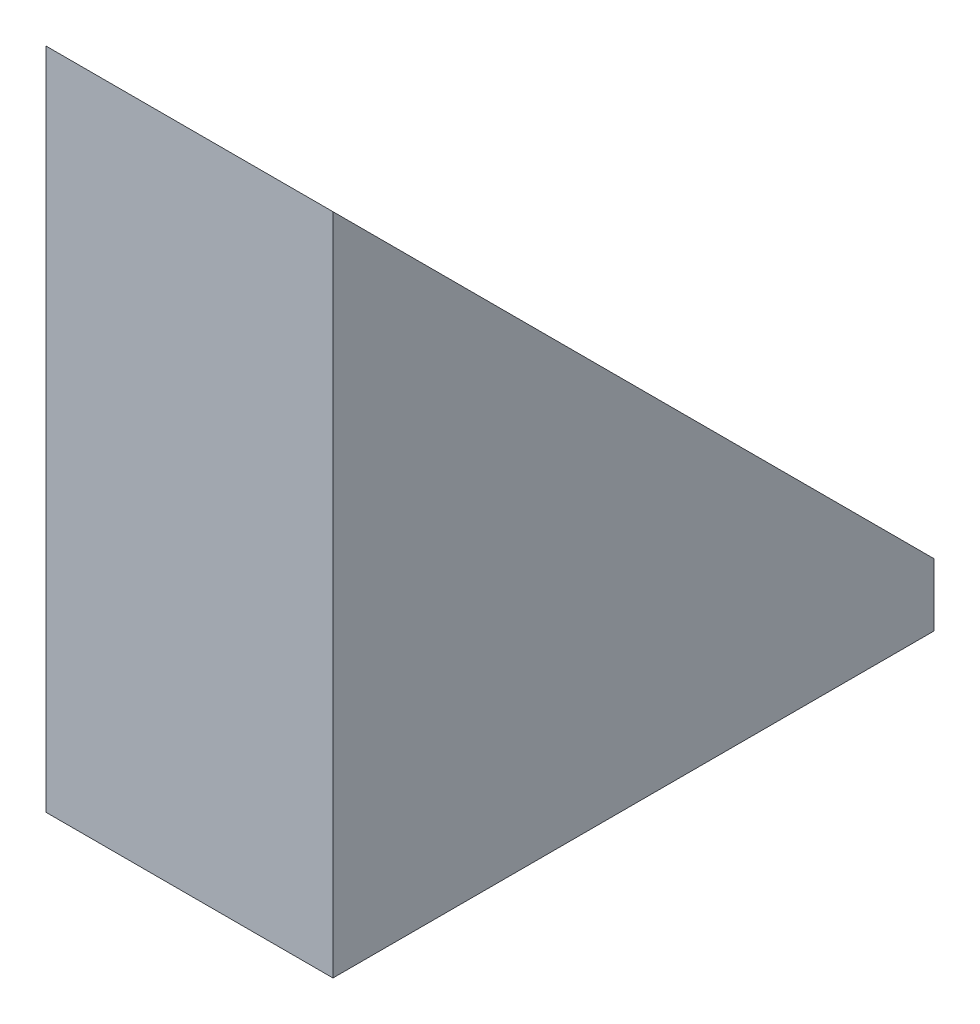
SolidWorks part; units mm, degrees
ref_plane "Plano frontal" through (0, 0, 0) normal (0, 0, 1) x (1, 0, 0)
ref_plane "Plano superior" through (0, 0, 0) normal (0, 1, 0) x (1, 0, 0)
ref_plane "Plano direito" through (0, 0, 0) normal (1, 0, 0) x (0, 0, -1)
sketch "Sketch1" plane through (-23229.7404, 0, 0) normal (-1, 0, 0) x (0, 0, 1)
  line L0 (40109.1002, 5310.5864) -> (40276.6536, 5478.1398)
  line L1 (40109.1002, 5293.1198) -> (40276.6536, 5293.1198)
  line L2 (40109.1002, 5293.1198) -> (40109.1002, 5310.5864)
  line L3 (40109.1002, 5310.5864) -> (40276.6536, 5310.5864)
  line L4 (40276.6536, 5293.1198) -> (40276.6536, 5310.5864)
  line L5 (40276.6536, 5478.1398) -> (40276.6536, 5310.5864)
  point P4 (40266.3788, 5450.5749)
  point P6 (40276.6536, 5478.1398)
  line M5 (40465.3041, 5293.1198) -> (40109.1002, 5293.1198)
  dimension "D1" = 45
extrude "Boss-Extrude1" add sketch "Sketch1" against normal blind 80 contours L5 L0 L3 | L4 L3 L2 M5
